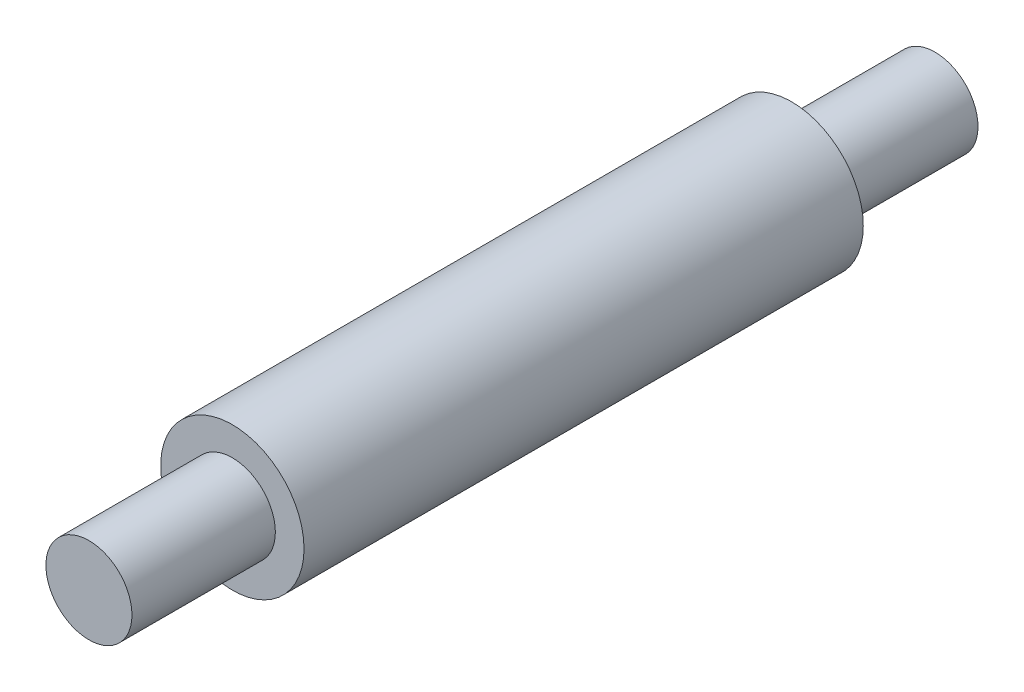
SolidWorks part; units mm, degrees
material "1060 Alloy"
ref_plane "Front Plane" through (0, 0, 0) normal (0, 0, 1) x (1, 0, 0)
ref_plane "Top Plane" through (0, 0, 0) normal (0, 1, 0) x (1, 0, 0)
ref_plane "Right Plane" through (0, 0, 0) normal (1, 0, 0) x (0, 0, -1)
sketch "Sketch6" plane through (0, 0, 0) normal (1, 0, 0) x (0, 0, -1)
  line L0 (0, 0) -> (59, 0)
  line L1 (59, 0) -> (59, 3)
  line L2 (59, 3) -> (49, 3)
  line L3 (49, 3) -> (49, 5)
  line L4 (49, 5) -> (10, 5)
  line L5 (10, 5) -> (10, 3)
  line L6 (10, 3) -> (0, 3)
  line L7 (0, 3) -> (0, 0)
  dimension "D1" = 10
  dimension "D2" = 3
  dimension "D3" = 5
  dimension "D4" = 39
revolve "Revolve1" add sketch "Sketch6" angle 360 about L0
